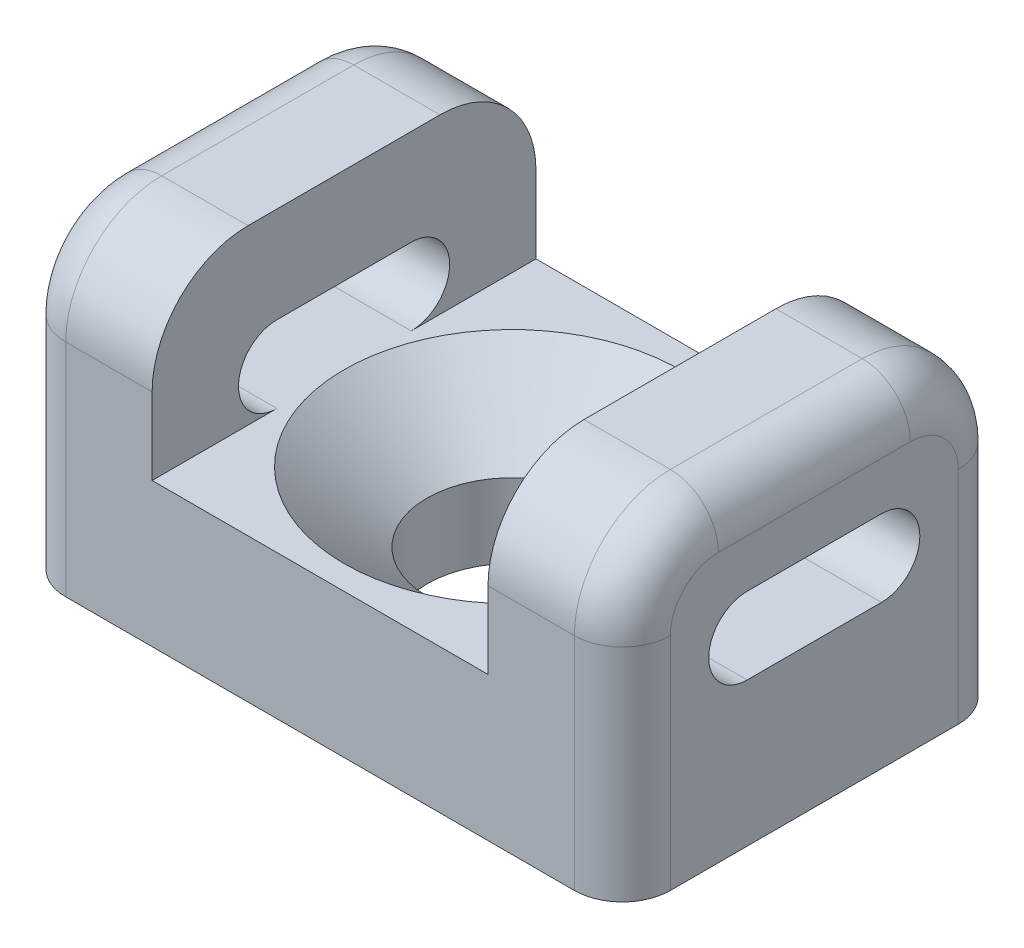
SolidWorks part; units mm, degrees
ref_plane "Front Plane" through (0, 0, 0) normal (0, 0, 1) x (1, 0, 0)
ref_plane "Top Plane" through (0, 0, 0) normal (0, 1, 0) x (1, 0, 0)
ref_plane "Right Plane" through (0, 0, 0) normal (1, 0, 0) x (0, 0, -1)
sketch "Sketch4" plane through (0, 0, 0) normal (0, 0, 1) x (1, 0, 0)
  line L0 (0, 0) -> (4.445, 0)
  line L1 (4.445, 0) -> (4.445, 4.572)
  line L2 (4.445, 4.572) -> (8.001, 4.572)
  line L3 (8.001, 4.572) -> (8.001, -3.81)
  line L4 (8.001, -3.81) -> (0, -3.81)
  line L5 (0, -3.81) -> (0, 0)
  line L6 (4.445, 2.032) -> (8.001, 2.032) construction
  point P9 (0, 0)
  dimension "D1" = 3.81
  dimension "D2" = 8.001
  dimension "D3" = 4.445
  dimension "D4" = 2.032
  dimension "D5" = 2.54
  dimension "D6" = 3.556
extrude "Boss-Extrude2" add sketch "Sketch4" along normal mid plane 10.16
hole_wizard "CSK for #8 Flat Head Machine Screw (100)2" positions "Sketch5" profile "Sketch6" countersink size "#8" standard "ANSI Inch" end condition through all
sketch "Sketch5" plane through (0, 0, 0) normal (0, 1, 0) x (1, 0, 0)
  point P0 (0, 0)
sketch "Sketch6" plane through (0, 0, 0) normal (1, 0, 0) x (0, 0, 1)
  line L0 (0, 0) -> (0, 3.81)
  line L1 (0, 3.81) -> (2.2479, 3.81)
  line L2 (2.2479, 3.81) -> (2.2479, 1.8436)
  line L3 (2.2479, 1.8436) -> (4.445, 0)
  line L5 (4.445, 0) -> (0, 0)
  line L6 (-2.2479, 1.8436) -> (-4.445, 0) construction
  line L11 (0, -6.35) -> (0, 107.95) construction
  dimension "Thru Hole Dia." = 4.4958
  dimension "Thru Hole Depth" = 3.81
  dimension "Near C'Sink Dia." = 8.89
  dimension "Near C'Sink Angle" = 100
sketch "Sketch7" plane through (4.445, 0, 0) normal (-1, 0, 0) x (0, 0, 1)
  line L0 (-1.778, 1.016) -> (1.778, 1.016) construction
  line L1 (-1.778, 2.032) -> (1.778, 2.032)
  line L2 (-1.778, 0) -> (1.778, 0)
  arc A0 (-1.778, 2.032) -> (-1.778, 0) centre (-1.778, 1.016) ccw
  arc A1 (1.778, 0) -> (1.778, 2.032) centre (1.778, 1.016) ccw
  point P2 (0, 1.016)
  dimension "D1" = 3.556
extrude "Cut-Extrude1" cut sketch "Sketch7" against normal through all
fillet "Fillet1" radius 2.54 2 edges at (6.223, 4.572, -5.08) (6.223, 4.572, 5.08)
fillet "Fillet2" radius 1.27 5 edges at (8.001, -0.889, -5.08) (8.001, 3.8281, -4.3361) (8.001, 4.572, 0) (8.001, 3.8281, 4.3361) (8.001, -0.889, 5.08)
mirror "Mirror2" about plane through (0, 0, 0) normal (1, 0, 0) of bodies 110
